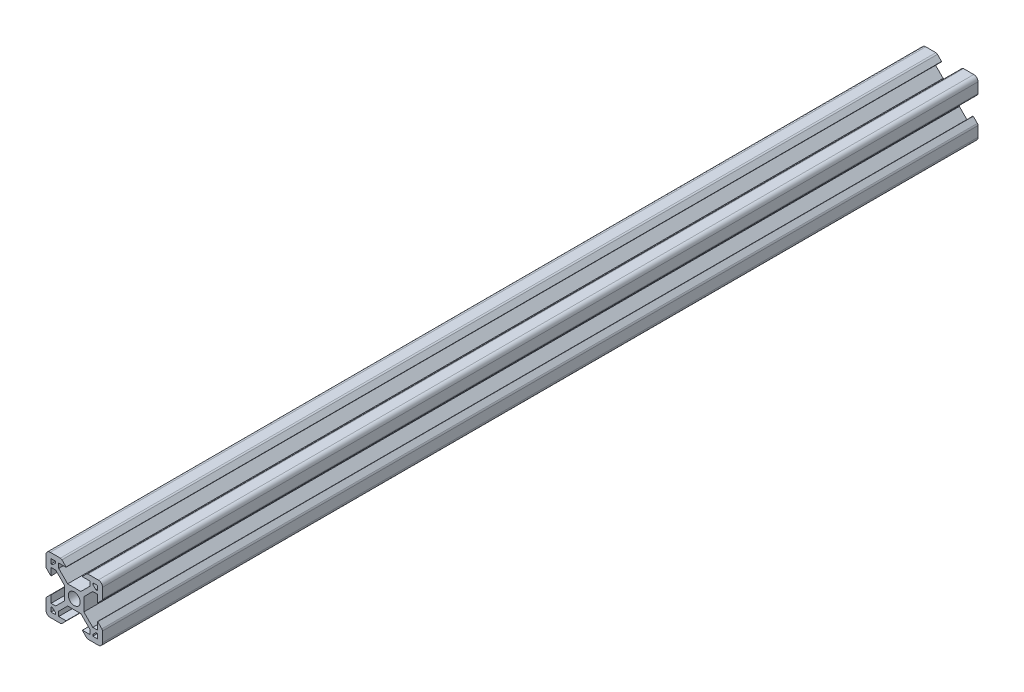
SolidWorks part; units mm, degrees
ref_plane "Front Plane" through (0, 0, 0) normal (0, 0, 1) x (1, 0, 0)
ref_plane "Top Plane" through (0, 0, 0) normal (0, 1, 0) x (1, 0, 0)
ref_plane "Right Plane" through (0, 0, 0) normal (1, 0, 0) x (0, 0, -1)
sketch "Sketch2" plane through (0, 0, 0) normal (0, 0, 1) x (1, 0, 0)
  line L0 (-8.2, 2.89) -> (-8.2, 5.5)
  line L1 (-2.1, 0) -> (-10, 0) construction
  line L2 (0, 2.1) -> (0, 10) construction
  line L3 (-4.9072, 10) -> (-8.5, 10)
  line L4 (-10, 4.9072) -> (-10, 8.5)
  line L5 (-2.1, 0) -> (-3.4, 0) construction
  line L6 (0, 2.1) -> (0, 3.4) construction
  line L7 (0, 3.4) -> (-2.3393, 3.4)
  line L8 (-3.4, 0) -> (-3.4, 2.3393)
  line L9 (-2.89, 8.2) -> (-5.5, 8.2)
  line L10 (-6.57, 8.2) -> (-6.57, 7.66)
  line L11 (-8.2, 6.57) -> (-7.66, 6.57)
  line L12 (-5.5, 8.2) -> (-5.5, 6.5607)
  line L13 (-6.5607, 5.5) -> (-8.2, 5.5)
  line L14 (-8.2, 8.2) -> (-1.4849, 1.4849) construction
  line L15 (-6.5607, 5.5) -> (-3.4, 2.3393)
  line L16 (-5.5, 6.5607) -> (-2.3393, 3.4)
  line L17 (-7.66, 6.57) -> (-6.57, 7.66)
  line L18 (-8.7303, 7.6697) -> (-0.5303, -0.5303) construction
  line L19 (-7.6697, 8.7303) -> (0.5303, 0.5303) construction
  line L20 (-8.2, 8.2) -> (0, 0) construction
  line L21 (-8.2, 6.57) -> (-8.2, 8.2)
  line L22 (-8.2, 0) -> (-8.2, 8.2) construction
  line L23 (-6.57, 8.2) -> (-8.2, 8.2)
  line L24 (0, 8.2) -> (-8.2, 8.2) construction
  line L25 (-10, 0) -> (-10, 10) construction
  line L26 (0, 10) -> (-10, 10) construction
  line L27 (-2.89, 8.31) -> (-2.89, 8.2)
  line L29 (-8.31, 2.89) -> (-8.2, 2.89)
  line L30 (-4.3486, 9.7686) -> (-2.89, 8.31)
  line L31 (-8.31, 2.89) -> (-9.7686, 4.3486)
  arc A0 (0, 2.1) -> (-2.1, 0) centre (0, 0) ccw
  arc A1 (-10, 8.5) -> (-8.5, 10) centre (-8.5, 8.5) cw
  arc A2 (-9.7686, 4.3486) -> (-10, 4.9072) centre (-9.21, 4.9072) cw
  arc A3 (-4.3486, 9.7686) -> (-4.9072, 10) centre (-4.9072, 9.21) ccw
  point P29 (-10, 10)
  point P39 (-10, 4.58)
  point P42 (-4.58, 10)
  dimension "D3" = 2.1
  dimension "D15" = 1.5
  dimension "D22" = 0.79
  dimension "D1" = 10
  dimension "D2" = 10
  dimension "D4" = 1.8
  dimension "D5" = 3.43
  dimension "D6" = 3.43
  dimension "D7" = 0.54
  dimension "D8" = 0.54
  dimension "D9" = 1.07
  dimension "D10" = 1.07
  dimension "D11" = 3.4
  dimension "D12" = 3.4
  dimension "D16" = 7.11
  dimension "D17" = 0.11
  dimension "D18" = 1.69
  dimension "D19" = 0.11
  dimension "D20" = 7.11
  dimension "D21" = 1.69
  dimension "D13" = 0.75
  dimension "D14" = 0.75
sketch "Sketch6" plane through (0, 0, 0) normal (0, 0, 1) x (1, 0, 0)
  line L0 (-3.4, 0) -> (-3.4, 2.3393) construction
  line L1 (-6.5607, 5.5) -> (-3.4, 2.3393) construction
  line L2 (-6.5607, 5.5) -> (-8.2, 5.5) construction
  line L3 (-8.2, 2.89) -> (-8.2, 5.5) construction
  line L4 (-8.31, 2.89) -> (-8.2, 2.89) construction
  line L5 (-7.66, 6.57) -> (-6.57, 7.66)
  line L6 (-6.57, 7.66) -> (-6.57, 8.2)
  line L7 (-6.57, 8.2) -> (-8.2, 8.2)
  line L8 (-8.2, 8.2) -> (-8.2, 6.57)
  line L9 (-8.2, 6.57) -> (-7.66, 6.57)
  line L10 (-7.66, 6.57) -> (-6.57, 7.66)
  line L11 (-6.57, 7.66) -> (-6.57, 8.2)
  line L12 (-6.57, 8.2) -> (-8.2, 8.2)
  line L13 (-8.2, 8.2) -> (-8.2, 6.57)
  line L14 (-8.2, 6.57) -> (-7.66, 6.57)
  line L15 (-8.31, 2.89) -> (-9.7686, 4.3486) construction
  line L16 (-10, 4.9072) -> (-10, 8.5) construction
  line L17 (-4.9072, 10) -> (-8.5, 10) construction
  line L18 (-4.3486, 9.7686) -> (-2.89, 8.31) construction
  line L19 (-2.89, 8.31) -> (-2.89, 8.2) construction
  line L20 (-2.89, 8.2) -> (-5.5, 8.2) construction
  line L21 (-5.5, 8.2) -> (-5.5, 6.5607) construction
  line L22 (-5.5, 6.5607) -> (-2.3393, 3.4) construction
  line L23 (0, 3.4) -> (-2.3393, 3.4) construction
  line L24 (-3.4, -2.3393) -> (-3.4, 2.3393)
  line L25 (-6.5607, 5.5) -> (-3.4, 2.3393)
  line L26 (-6.5607, 5.5) -> (-8.2, 5.5)
  line L27 (-8.2, 2.89) -> (-8.2, 5.5)
  line L28 (-8.31, 2.89) -> (-8.2, 2.89)
  line L29 (-8.31, 2.89) -> (-9.7686, 4.3486)
  line L30 (-10, 4.9072) -> (-10, 8.5)
  line L31 (-4.9072, 10) -> (-8.5, 10)
  line L32 (-4.3486, 9.7686) -> (-2.89, 8.31)
  line L33 (-2.89, 8.31) -> (-2.89, 8.2)
  line L34 (-2.89, 8.2) -> (-5.5, 8.2)
  line L35 (-5.5, 8.2) -> (-5.5, 6.5607)
  line L36 (-5.5, 6.5607) -> (-2.3393, 3.4)
  line L37 (2.3393, 3.4) -> (-2.3393, 3.4)
  line L38 (0, 2.1) -> (0, 10) construction
  line L39 (-2.1, 0) -> (-10, 0) construction
  line L40 (0, 2.1) -> (0, 10) construction
  line L41 (-2.1, 0) -> (-10, 0) construction
  line L42 (2.1, 0) -> (10, 0) construction
  line L43 (5.5, 6.5607) -> (2.3393, 3.4)
  line L44 (5.5, 8.2) -> (5.5, 6.5607)
  line L45 (2.89, 8.2) -> (5.5, 8.2)
  line L46 (2.89, 8.31) -> (2.89, 8.2)
  line L47 (4.3486, 9.7686) -> (2.89, 8.31)
  line L48 (4.9072, 10) -> (8.5, 10)
  line L49 (10, 4.9072) -> (10, 8.5)
  line L50 (8.31, 2.89) -> (9.7686, 4.3486)
  line L51 (8.31, 2.89) -> (8.2, 2.89)
  line L52 (8.2, 2.89) -> (8.2, 5.5)
  line L53 (6.5607, 5.5) -> (8.2, 5.5)
  line L54 (6.5607, 5.5) -> (3.4, 2.3393)
  line L55 (3.4, -2.3393) -> (3.4, 2.3393)
  line L56 (8.2, 6.57) -> (7.66, 6.57)
  line L57 (8.2, 8.2) -> (8.2, 6.57)
  line L58 (6.57, 8.2) -> (8.2, 8.2)
  line L59 (6.57, 7.66) -> (6.57, 8.2)
  line L60 (7.66, 6.57) -> (6.57, 7.66)
  line L61 (0, -2.1) -> (0, -10) construction
  line L62 (7.66, -6.57) -> (6.57, -7.66)
  line L63 (6.57, -7.66) -> (6.57, -8.2)
  line L64 (6.57, -8.2) -> (8.2, -8.2)
  line L65 (8.2, -8.2) -> (8.2, -6.57)
  line L66 (8.2, -6.57) -> (7.66, -6.57)
  line L67 (6.5607, -5.5) -> (3.4, -2.3393)
  line L68 (6.5607, -5.5) -> (8.2, -5.5)
  line L69 (8.2, -2.89) -> (8.2, -5.5)
  line L70 (8.31, -2.89) -> (8.2, -2.89)
  line L71 (8.31, -2.89) -> (9.7686, -4.3486)
  line L72 (10, -4.9072) -> (10, -8.5)
  line L73 (4.9072, -10) -> (8.5, -10)
  line L74 (4.3486, -9.7686) -> (2.89, -8.31)
  line L75 (2.89, -8.31) -> (2.89, -8.2)
  line L76 (2.89, -8.2) -> (5.5, -8.2)
  line L77 (5.5, -8.2) -> (5.5, -6.5607)
  line L78 (5.5, -6.5607) -> (2.3393, -3.4)
  line L79 (2.3393, -3.4) -> (-2.3393, -3.4)
  line L80 (-5.5, -6.5607) -> (-2.3393, -3.4)
  line L81 (-5.5, -8.2) -> (-5.5, -6.5607)
  line L82 (-2.89, -8.2) -> (-5.5, -8.2)
  line L83 (-2.89, -8.31) -> (-2.89, -8.2)
  line L84 (-4.3486, -9.7686) -> (-2.89, -8.31)
  line L85 (-4.9072, -10) -> (-8.5, -10)
  line L86 (-10, -4.9072) -> (-10, -8.5)
  line L87 (-8.31, -2.89) -> (-9.7686, -4.3486)
  line L88 (-8.31, -2.89) -> (-8.2, -2.89)
  line L89 (-8.2, -2.89) -> (-8.2, -5.5)
  line L90 (-6.5607, -5.5) -> (-8.2, -5.5)
  line L91 (-6.5607, -5.5) -> (-3.4, -2.3393)
  line L92 (-8.2, -6.57) -> (-7.66, -6.57)
  line L93 (-8.2, -8.2) -> (-8.2, -6.57)
  line L94 (-6.57, -8.2) -> (-8.2, -8.2)
  line L95 (-6.57, -7.66) -> (-6.57, -8.2)
  line L96 (-7.66, -6.57) -> (-6.57, -7.66)
  arc A0 (0, 2.1) -> (-2.1, 0) centre (0, 0) ccw construction
  arc A1 (-10, 4.9072) -> (-9.7686, 4.3486) centre (-9.21, 4.9072) ccw construction
  arc A2 (-8.5, 10) -> (-10, 8.5) centre (-8.5, 8.5) ccw construction
  arc A3 (-4.3486, 9.7686) -> (-4.9072, 10) centre (-4.9072, 9.21) ccw construction
  circle A4 centre (0, 0) radius 2.1
  arc A5 (-10, 4.9072) -> (-9.7686, 4.3486) centre (-9.21, 4.9072) ccw
  arc A6 (-8.5, 10) -> (-10, 8.5) centre (-8.5, 8.5) ccw
  arc A7 (-4.3486, 9.7686) -> (-4.9072, 10) centre (-4.9072, 9.21) ccw
  arc A8 (4.3486, 9.7686) -> (4.9072, 10) centre (4.9072, 9.21) cw
  arc A9 (8.5, 10) -> (10, 8.5) centre (8.5, 8.5) cw
  arc A10 (10, 4.9072) -> (9.7686, 4.3486) centre (9.21, 4.9072) cw
  arc A11 (10, -4.9072) -> (9.7686, -4.3486) centre (9.21, -4.9072) ccw
  arc A12 (8.5, -10) -> (10, -8.5) centre (8.5, -8.5) ccw
  arc A13 (4.3486, -9.7686) -> (4.9072, -10) centre (4.9072, -9.21) ccw
  arc A14 (-4.3486, -9.7686) -> (-4.9072, -10) centre (-4.9072, -9.21) cw
  arc A15 (-8.5, -10) -> (-10, -8.5) centre (-8.5, -8.5) cw
  arc A16 (-10, -4.9072) -> (-9.7686, -4.3486) centre (-9.21, -4.9072) cw
  point P85 (3.4, 0)
  dimension "D1" = 0
extrude "Boss-Extrude1" add sketch "Sketch6" against normal blind 310
ref_plane "Middle" through (0, 0, -155) normal (0, 0, 1) x (1, 0, 0)
